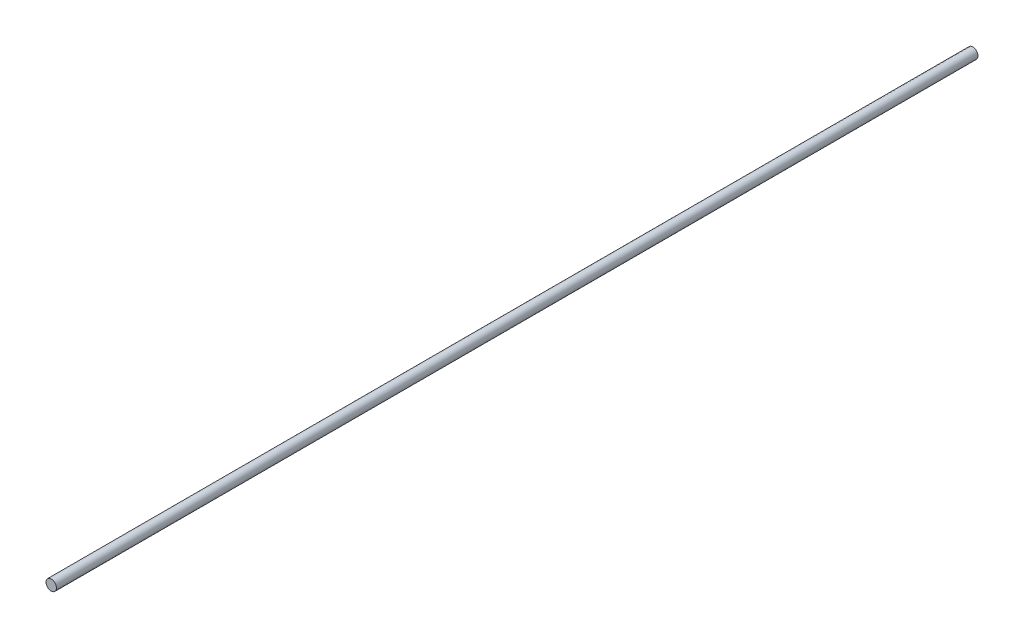
SolidWorks part; units mm, degrees
material "Plain Carbon Steel"
ref_plane "Front Plane" through (0, 0, 0) normal (0, 0, 1) x (1, 0, 0)
ref_plane "Top Plane" through (0, 0, 0) normal (0, 1, 0) x (1, 0, 0)
ref_plane "Right Plane" through (0, 0, 0) normal (1, 0, 0) x (0, 0, -1)
sketch "Sketch1" plane through (0, 0, 0) normal (0, 0, 1) x (1, 0, 0)
  circle A0 centre (0, 0) radius 3.9688
extrude "Boss-Extrude1" add sketch "Sketch1" against normal blind 700
